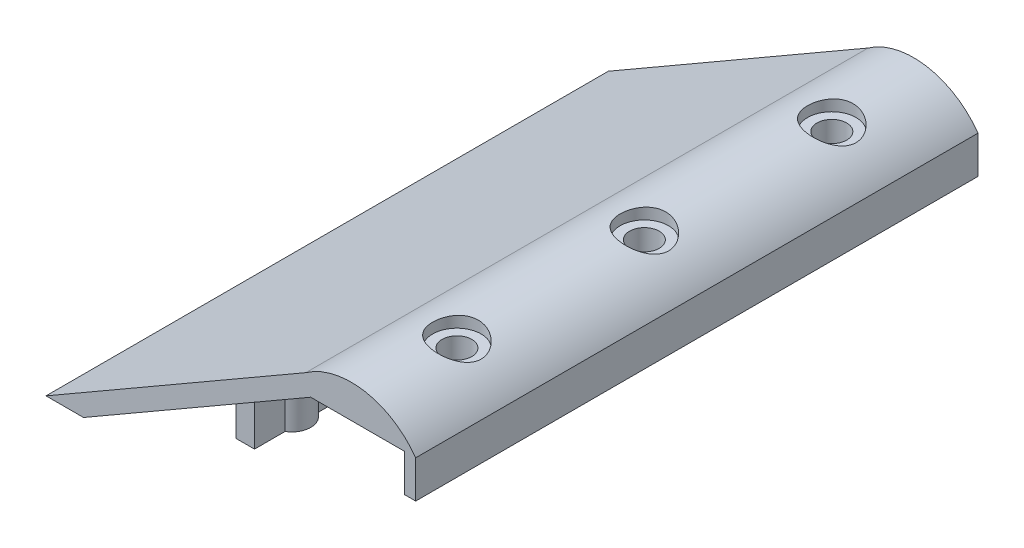
SolidWorks part; units mm, degrees
ref_plane "Alzado" through (0, 0, 0) normal (0, 0, 1) x (1, 0, 0)
ref_plane "Planta" through (0, 0, 0) normal (0, 1, 0) x (1, 0, 0)
ref_plane "Vista lateral" through (0, 0, 0) normal (1, 0, 0) x (0, 0, -1)
sketch "Croquis1" plane through (0, 0, 0) normal (0, 0, 1) x (1, 0, 0)
  line L0 (0, 34.3848) -> (0, -4.3701) construction
  line L1 (-35.1904, 0) -> (25, 0) construction
  line L2 (0, 0) -> (25, 0)
  line L3 (25, 0) -> (25, 5) construction
  line L4 (25, 5) -> (-1.3397, 5) construction
  line L5 (-1.3397, 5) -> (-70.6218, -35)
  line L6 (-70.6218, -35) -> (-60.6218, -35)
  line L7 (-60.6218, -35) -> (0, 0)
  line L8 (-73.772, -35) -> (41.2109, -35) construction
  line L9 (34.3149, -26) -> (-26.4016, -26) construction
  line L10 (-77.6138, -56) -> (49.339, -56) construction
  line L11 (0, 0) -> (25, 0) construction
  line L12 (0, 0) -> (25, 0)
  line L13 (0, 0) -> (25, 0)
  line L14 (25, 0) -> (25, -10)
  line L15 (25, -10) -> (28, -10)
  line L16 (28, -10) -> (28, 0)
  line L17 (-4.6669, 0) -> (44.3879, 0) construction
  arc A0 (-1.3397, 5) -> (28, 0) centre (10.8301, -12.1699) cw
  dimension "D8" = 10
  dimension "D10" = 21.0454
  dimension "D1" = 25
  dimension "D2" = 30
  dimension "D3" = 5
  dimension "D4" = 5
  dimension "D5" = 26
  dimension "D6" = 30
  dimension "D7" = 35
  dimension "D9" = 3
extrude "Saliente-Extruir1" add sketch "Croquis1" along normal mid plane 150 contours A0 L5 L6 L7 L2 L14 L15 L16
ref_plane "Plano Tangente Para Perforacion" through (0, 8.8756, 0) normal (0, 1, 0) x (1, 0, 0)
ref_plane "Bases Soporte" through (0, -15, 0) normal (0, 1, 0) x (1, 0, 0)
sketch "Croquis2" plane through (0, -15, 0) normal (0, 1, 0) x (1, 0, 0)
  line L0 (122.6306, 0) -> (-182.6306, 0) construction
  line L1 (0, 52.1261) -> (0, -47.2849) construction
  line L2 (-30, 99.6856) -> (-30, -100.7612) construction
  line L3 (-32.5, 4.3301) -> (-32.5, 12.5)
  line L4 (-32.5, -12.5) -> (-27.5, -12.5)
  line L5 (-32.5, -12.5) -> (-32.5, -4.3301)
  line L6 (-32.5, 12.5) -> (-27.5, 12.5)
  line L7 (-27.5, -12.5) -> (-27.5, -4.3301)
  line L8 (-32.5, -12.5) -> (-27.5, 12.5) construction
  line L9 (-32.5, 12.5) -> (-27.5, -12.5) construction
  line L10 (-27.5, 4.3301) -> (-27.5, 12.5)
  line L17 (-32.5, 54.3301) -> (-32.5, 62.5)
  line L24 (-32.5, 37.5) -> (-27.5, 37.5)
  line L25 (-32.5, 37.5) -> (-32.5, 45.6699)
  line L26 (-32.5, 62.5) -> (-27.5, 62.5)
  line L27 (-27.5, 37.5) -> (-27.5, 45.6699)
  line L28 (-27.5, 54.3301) -> (-27.5, 62.5)
  line L29 (-32.5, 37.5) -> (-27.5, 62.5) construction
  line L30 (-32.5, 62.5) -> (-27.5, 37.5) construction
  line L31 (-32.5, 4.3301) -> (-32.5, 54.3301) construction
  line L32 (-32.5, -45.6699) -> (-32.5, -37.5)
  line L33 (-32.5, -62.5) -> (-27.5, -62.5)
  line L34 (-32.5, -62.5) -> (-32.5, -54.3301)
  line L35 (-32.5, -37.5) -> (-27.5, -37.5)
  line L36 (-27.5, -62.5) -> (-27.5, -54.3301)
  line L37 (-27.5, -45.6699) -> (-27.5, -37.5)
  line L38 (-32.5, -62.5) -> (-27.5, -37.5) construction
  line L39 (-32.5, -37.5) -> (-27.5, -62.5) construction
  line L40 (-32.5, 4.3301) -> (-32.5, -45.6699) construction
  arc A0 (-32.5, 4.3301) -> (-32.5, -4.3301) centre (-30, 0) ccw
  arc A2 (-27.5, -4.3301) -> (-27.5, 4.3301) centre (-30, 0) ccw
  arc A6 (-32.5, 54.3301) -> (-32.5, 45.6699) centre (-30, 50) ccw
  arc A7 (-27.5, 45.6699) -> (-27.5, 54.3301) centre (-30, 50) ccw
  arc A8 (-32.5, -45.6699) -> (-32.5, -54.3301) centre (-30, -50) ccw
  arc A9 (-27.5, -54.3301) -> (-27.5, -45.6699) centre (-30, -50) ccw
  dimension "D1" = 10
  dimension "D2" = 30
  dimension "D3" = 5
  dimension "D4" = 25
  dimension "D5" = 2
  dimension "D6" = 50
  dimension "D8" = 50
  dimension "D7" = 2
extrude "Saliente-Extruir2" add sketch "Croquis2" against normal blind 17 and the other way up to surface
sketch "Croquis3" plane through (0, 8.8756, 0) normal (0, 1, 0) x (1, 0, 0)
  line L0 (0, -113.8566) -> (0, 103.3108) construction
  line L1 (55.4509, 0) -> (-87.9325, 0) construction
  line L2 (14, 0) -> (14, 50) construction
  line L3 (14, 0) -> (14, -50) construction
  line L6 (28, 75) -> (-1.3397, 75)
  line L7 (-1.3397, 75) -> (-1.3397, -75)
  line L8 (-1.3397, -75) -> (28, -75)
  line L9 (28, -75) -> (28, 75)
  line L10 (28, 75) -> (-1.3397, 75)
  line L11 (-1.3397, 75) -> (-1.3397, -75)
  line L12 (-1.3397, -75) -> (28, -75)
  line L13 (28, -75) -> (28, 75)
  circle A0 centre (14, 0) radius 3.9687
  circle A1 centre (14, 50) radius 3.9688
  circle A2 centre (14, -50) radius 3.9687
  dimension "D3" = 7.9375
  dimension "D2" = 14
  dimension "D5" = 50
  dimension "D7" = 50
  dimension "D1" = 0
  dimension "D4" = 2
  dimension "D6" = 2
extrude "Cortar-Extruir1" cut sketch "Croquis3" against normal blind 10 contours A2 | A0 | A1
sketch "Croquis4" plane through (0, 8.8756, 0) normal (0, 1, 0) x (1, 0, 0)
  circle A0 centre (14, 50) radius 3.9688 construction
  circle A1 centre (14, -50) radius 3.9688 construction
  circle A2 centre (14, 0) radius 3.9687 construction
  circle A3 centre (14, 50) radius 3.9688
  circle A4 centre (14, -50) radius 3.9688
  circle A5 centre (14, 0) radius 3.9687
  circle A6 centre (14, 50) radius 6.4688
  circle A7 centre (14, 0) radius 6.4688
  circle A8 centre (14, -50) radius 6.4688
  dimension "D1" = 2.5
extrude "Cortar-Extruir2" cut sketch "Croquis4" against normal blind 3
ref_plane "Mordazas" through (0, -35, 0) normal (0, -1, 0) x (-1, 0, 0)
sketch "Croquis7" plane through (0, -35, 0) normal (0, -1, 0) x (-1, 0, 0)
  line L0 (-54.6749, 0) -> (103.8779, 0) construction
  line L1 (50.6218, -79.2787) -> (50.6218, 99.1128) construction
  line L2 (70.6218, -75) -> (70.6218, 75) construction
  line L3 (50.6218, 0) -> (50.6218, 50) construction
  line L4 (50.6218, 0) -> (50.6218, -50) construction
  circle A0 centre (50.6218, 0) radius 1.9844
  circle A1 centre (50.6218, 50) radius 1.9844
  circle A2 centre (50.6218, -50) radius 1.9844
  dimension "D2" = 3.9688
  dimension "D1" = 20
  dimension "D4" = 50
  dimension "D6" = 50
  dimension "D3" = 2
  dimension "D5" = 2
extrude "Saliente-Extruir3" add sketch "Croquis7" against normal up to surface (5.7735 mm away)
sketch "Croquis8" plane through (0, 0, 0) normal (0, 0, 1) x (1, 0, 0)
  line L0 (37.632, 0) -> (-83.7339, 0) construction
  line L1 (-50.6218, 18.5207) -> (-50.6218, -41.8553) construction
  line L2 (-52.6062, -30.3722) -> (-52.6062, -35) construction
  line L3 (-52.6062, -30.3722) -> (-52.6062, -35)
  line L4 (-52.6062, -30.3722) -> (-48.6374, -28.0808) construction
  line L5 (-52.6062, -30.3722) -> (-48.6374, -28.0808)
  line L6 (-48.6374, -35) -> (-48.6374, -28.0808) construction
  line L7 (-48.6374, -35) -> (-48.6374, -28.0808)
  line L8 (-52.6062, -35) -> (-48.6374, -35) construction
  line L9 (-52.6062, -35) -> (-48.6374, -35)
  line L11 (-53.6079, -33.5) -> (-47.5693, -33.5) construction
  arc A0 (-52.6062, -33.5) -> (-48.6374, -33.5) centre (-50.6218, -32.9374) ccw
  point P9 (-50.6218, -35)
  dimension "D1" = 1.5
extrude "Cortar-Extruir3" cut sketch "Croquis8" against normal mid plane 150
sketch "Croquis9" plane through (0, -32, 0) normal (0, -1, 0) x (1, 0, 0)
  line L0 (42.5355, 0) -> (-78.3445, 0) construction
  line L1 (-30, 66.7523) -> (-30, -66.0993) construction
  line L2 (-30, 0) -> (-30, 50) construction
  line L3 (-30, 0) -> (-30, -50) construction
  line L7 (-27.5, -12.5) -> (-27.5, -4.3301)
  line L8 (-27.5, 4.3301) -> (-27.5, 12.5)
  line L9 (-27.5, 12.5) -> (-32.5, 12.5)
  line L10 (-32.5, 12.5) -> (-32.5, 4.3301)
  line L11 (-32.5, -4.3301) -> (-32.5, -12.5)
  line L12 (-32.5, -12.5) -> (-27.5, -12.5)
  line L13 (-27.5, -12.5) -> (-27.5, -4.3301)
  line L14 (-27.5, 4.3301) -> (-27.5, 12.5)
  line L15 (-27.5, 12.5) -> (-32.5, 12.5)
  line L16 (-32.5, 12.5) -> (-32.5, 4.3301)
  line L17 (-32.5, -4.3301) -> (-32.5, -12.5)
  line L18 (-32.5, -12.5) -> (-27.5, -12.5)
  circle A0 centre (-30, 0) radius 1
  circle A1 centre (-30, 50) radius 1
  arc A2 (-27.5, -4.3301) -> (-27.5, 4.3301) centre (-30, 0) ccw
  arc A3 (-32.5, 4.3301) -> (-32.5, -4.3301) centre (-30, 0) ccw
  arc A4 (-27.5, -4.3301) -> (-27.5, 4.3301) centre (-30, 0) ccw
  arc A5 (-32.5, 4.3301) -> (-32.5, -4.3301) centre (-30, 0) ccw
  circle A6 centre (-30, -50) radius 1
  dimension "D2" = 2
  dimension "D4" = 50
  dimension "D6" = 50
  dimension "D1" = 0
  dimension "D3" = 2
  dimension "D5" = 2
extrude "Cortar-Extruir4" cut sketch "Croquis9" against normal blind 10 contours A0 | A1 | A6
